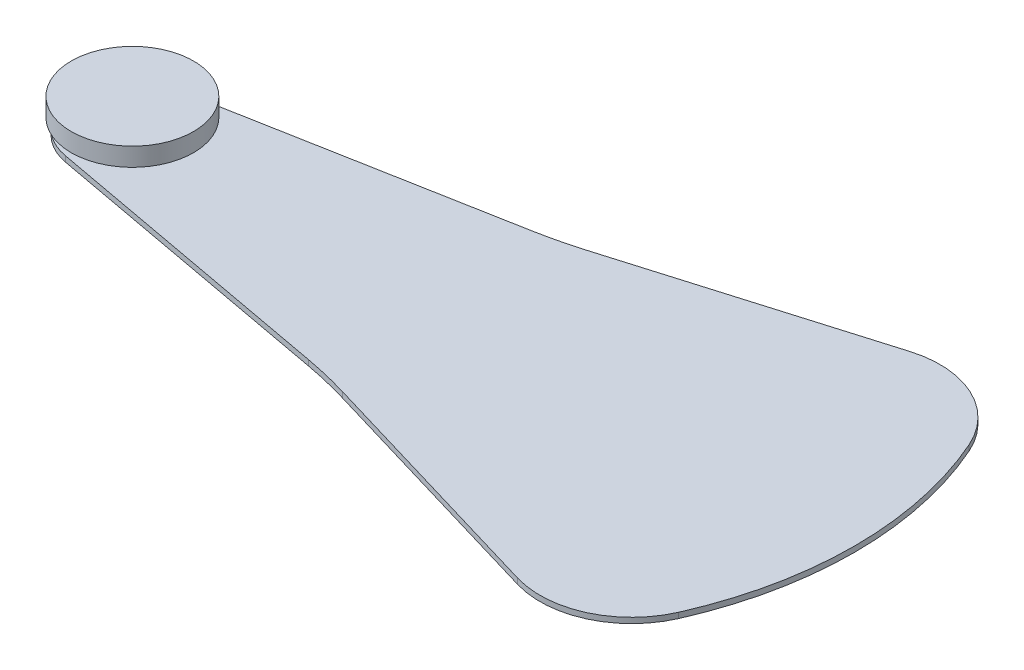
SolidWorks part; units mm, degrees
other "Camera1"
ref_plane "Front Plane" through (0, 0, 0) normal (0, 0, 1) x (1, 0, 0)
ref_plane "Top Plane" through (0, 0, 0) normal (0, 1, 0) x (1, 0, 0)
ref_plane "Right Plane" through (0, 0, 0) normal (1, 0, 0) x (0, 0, -1)
sketch "Sketch2" plane through (0, 113.481, 0) normal (0, -1, 0) x (1, 0, 0)
  line L0 (60.3729, 72.1945) -> (70.1254, 70.3945) construction
  line L1 (71.5841, 70.0445) -> (79.7331, 67.6273) construction
  line L2 (79.7331, 80.4618) -> (71.5841, 78.0445) construction
  line L3 (70.1254, 77.6946) -> (60.3729, 75.8945) construction
  line L4 (60.3729, 72.1945) -> (70.1254, 70.3945)
  line L5 (71.5841, 70.0445) -> (79.7331, 67.6273)
  line L6 (79.7331, 80.4618) -> (71.5841, 78.0445)
  line L7 (70.1254, 77.6946) -> (60.3729, 75.8945)
  arc A0 (60.3729, 75.8945) -> (60.3729, 72.1945) centre (60.7143, 74.0445) ccw construction
  arc A1 (71.5841, 70.0445) -> (70.1254, 70.3945) centre (67.5519, 56.4514) ccw construction
  arc A2 (79.7331, 67.6273) -> (83.3331, 69.2945) centre (80.5866, 70.5046) ccw construction
  arc A3 (83.3331, 69.2945) -> (84.3331, 74.0445) centre (72.5519, 74.0445) ccw construction
  arc A4 (84.3331, 74.0445) -> (83.3331, 78.7945) centre (72.5519, 74.0445) ccw construction
  arc A5 (83.3331, 78.7945) -> (79.7331, 80.4618) centre (80.5866, 77.5845) ccw construction
  arc A6 (70.1254, 77.6946) -> (71.5841, 78.0445) centre (67.5519, 91.6377) ccw construction
  arc A7 (60.3729, 75.8945) -> (60.3729, 72.1945) centre (60.7143, 74.0445) ccw
  arc A8 (71.5841, 70.0445) -> (70.1254, 70.3945) centre (67.5519, 56.4514) ccw
  arc A9 (79.7331, 67.6273) -> (83.3331, 69.2945) centre (80.5866, 70.5046) ccw
  arc A10 (83.3331, 69.2945) -> (84.3331, 74.0445) centre (72.5519, 74.0445) ccw
  arc A11 (84.3331, 74.0445) -> (83.3331, 78.7945) centre (72.5519, 74.0445) ccw
  arc A12 (83.3331, 78.7945) -> (79.7331, 80.4618) centre (80.5866, 77.5845) ccw
  arc A13 (70.1254, 77.6946) -> (71.5841, 78.0445) centre (67.5519, 91.6377) ccw
extrude "Boss-Extrude2" add sketch "Sketch2" against normal up to surface (0.18 mm away)
sketch "Sketch4" plane through (0, 113.481, 0) normal (0, -1, 0) x (1, 0, 0)
  circle A0 centre (60.7143, 74.0445) radius 1
  point P3 (61.7143, 74.0445)
  dimension "D1" = 2
extrude "Cut-Extrude1" cut sketch "Sketch4" against normal through all
ref_plane "Plane3" through (0, 113.991, 0) normal (0, 1, 0) x (1, 0, 0)
sketch "Sketch7" plane through (0, 113.991, 0) normal (0, 1, 0) x (1, 0, 0)
  circle A0 centre (60.7143, -74.0445) radius 2
  dimension "D1" = 4
extrude "Boss-Extrude3" add sketch "Sketch7" along normal blind 0.6 separate body
sketch "Sketch8" plane through (0, 113.661, 0) normal (0, 1, 0) x (1, 0, 0)
  circle A1 centre (60.7143, -74.0445) radius 1 construction
  circle A2 centre (60.7143, -74.0445) radius 1.4
  circle A3 centre (60.7143, -74.0445) radius 1.4
  circle A4 centre (60.7143, -74.0445) radius 1
  dimension "D1" = 0.4
extrude "Boss-Extrude4" add sketch "Sketch8" along normal up to next (0.93 mm away)
